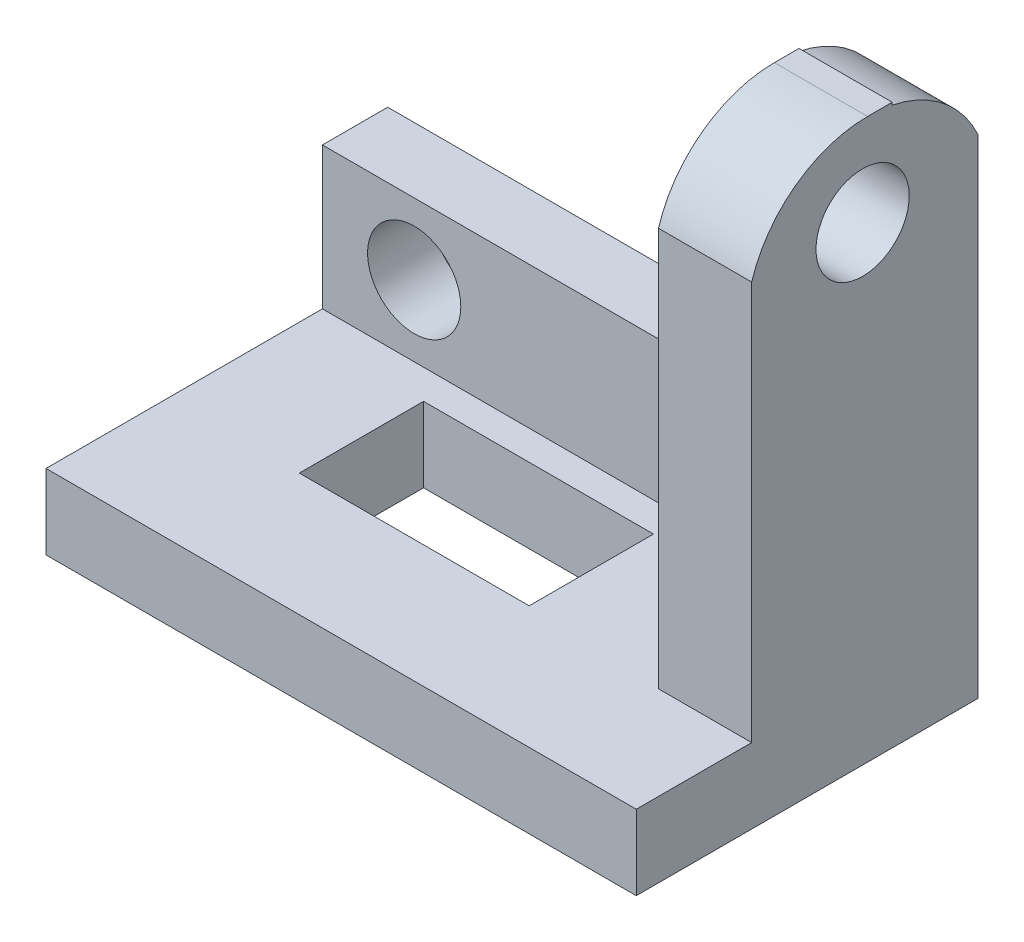
SolidWorks part; units mm, degrees
ref_plane "Front Plane" through (0, 0, 0) normal (0, 0, 1) x (1, 0, 0)
ref_plane "Top Plane" through (0, 0, 0) normal (0, 1, 0) x (1, 0, 0)
ref_plane "Right Plane" through (0, 0, 0) normal (1, 0, 0) x (0, 0, -1)
sketch "Sketch9" plane through (0, 0, 0) normal (0, 1, 0) x (1, 0, 0)
  line L1 (-38.1089, 7.0917) -> (56.8911, 7.0917)
  line L2 (-38.1089, 7.0917) -> (-38.1089, -47.9083)
  line L3 (-38.1089, -47.9083) -> (56.8911, -47.9083)
  line L4 (56.8911, 7.0917) -> (56.8911, -47.9083)
  dimension "D1" = 95
  dimension "D2" = 55
extrude "Boss-Extrude1" add sketch "Sketch9" against normal blind 90
sketch "Sketch10" plane through (56.8911, 0, 0) normal (1, 0, 0) x (0, 0, -1)
  line L0 (7.0917, -90) -> (7.0917, -77.946)
  line L1 (7.0917, -90) -> (7.0917, 0) construction
  line L2 (7.0917, -77.946) -> (-18.0702, -77.946)
  line L4 (7.0917, -77.946) -> (7.0917, -16.7302)
  line L6 (7.0917, -16.7302) -> (7.0917, -11.4164)
  line L7 (-18.0702, -77.946) -> (-29.3356, -77.946)
  line L8 (-47.9083, -90) -> (-47.9083, 0) construction
  line L9 (-47.9083, -77.946) -> (-47.9083, 0)
  line L10 (-47.9083, 0) -> (-47.9083, 6.5304)
  line L12 (-29.3356, -77.946) -> (-29.3356, -13.7545)
  line L13 (7.0917, -16.7302) -> (7.0917, -77.946)
  line L14 (-47.9083, 6.5304) -> (-6.7174, 6.5304)
  line L15 (-6.7174, 6.5304) -> (-6.7174, -0.4053)
  line L16 (-29.3356, -13.7545) -> (-29.3356, -77.946)
  line L17 (-47.9083, -77.946) -> (-29.3356, -77.946)
  arc A1 (-29.3356, -13.7545) -> (7.0917, -11.4164) centre (-10.6759, -19.5343) cw
  arc A2 (-6.7174, -0.4053) -> (-29.3356, -13.7545) centre (-10.6759, -19.5343) ccw
  line M1 (7.0917, 0) -> (-47.9083, 0)
  line M2 (-47.9083, 0) -> (-47.9083, -90)
  line M4 (7.0917, -90) -> (7.0917, 0)
extrude "Cut-Extrude5" cut sketch "Sketch10" against normal blind 100 contours L15 A1 M4 M1 | L12 A1 L17 M1 M2
sketch "Sketch12" plane through (-38.1089, 0, 0) normal (-1, 0, 0) x (0, 0, 1)
  line L1 (38.1456, -55.1005) -> (-22.3412, -55.1005)
  line L2 (38.1456, -55.1005) -> (38.1456, 18.7531)
  line L3 (38.1456, 18.7531) -> (-22.3412, 18.7531)
  line L4 (-22.3412, -55.1005) -> (-22.3412, 18.7531)
extrude "Cut-Extrude7" cut sketch "Sketch12" against normal blind 80
sketch "Sketch13" plane through (0, -55.1005, 0) normal (0, 1, 0) x (1, 0, 0)
  line L0 (-38.1089, 7.0917) -> (-38.1089, -29.3356) construction
  line L1 (-38.1089, -3.4179) -> (41.8911, -3.4179)
  line L2 (-38.1089, -3.4179) -> (-38.1089, -29.3356)
  line L3 (-38.1089, -29.3356) -> (41.8911, -29.3356)
  line L4 (41.8911, -3.4179) -> (41.8911, -29.3356)
extrude "Cut-Extrude8" cut sketch "Sketch13" against normal up to surface (22.8455 mm away) up to face at (9.3911, -77.946, 38.622)
fillet "Fillet1" radius 20 1 edges at (41.8911, -55.1005, -1.8369)
sketch "Sketch16" plane through (0, 0, 3.4179) normal (0, 0, 1) x (1, 0, 0)
  circle A0 centre (-23.3423, -66.5232) radius 7.5
  circle A1 centre (27.0332, -66.5232) radius 7.5
  dimension "D1" = 15
  dimension "D2" = 50.3755
extrude "Cut-Extrude9" cut sketch "Sketch16" against normal blind 30 contours A0 | A1
sketch "Sketch17" plane through (0, -77.946, 0) normal (0, 1, 0) x (1, 0, 0)
  line L1 (-17.0782, -8.1721) -> (19.9218, -8.1721)
  line L2 (-17.0782, -8.1721) -> (-17.0782, -28.1721)
  line L3 (-17.0782, -28.1721) -> (19.9218, -28.1721)
  line L4 (19.9218, -8.1721) -> (19.9218, -28.1721)
  dimension "D1" = 20
  dimension "D2" = 37
extrude "Cut-Extrude10" cut sketch "Sketch17" against normal blind 30
sketch "Sketch18" plane through (41.8911, 0, 0) normal (-1, 0, 0) x (0, 0, 1)
  circle A0 centre (11.481, -14.3921) radius 7.5
  dimension "D1" = 15
extrude "Cut-Extrude11" cut sketch "Sketch18" against normal blind 30
